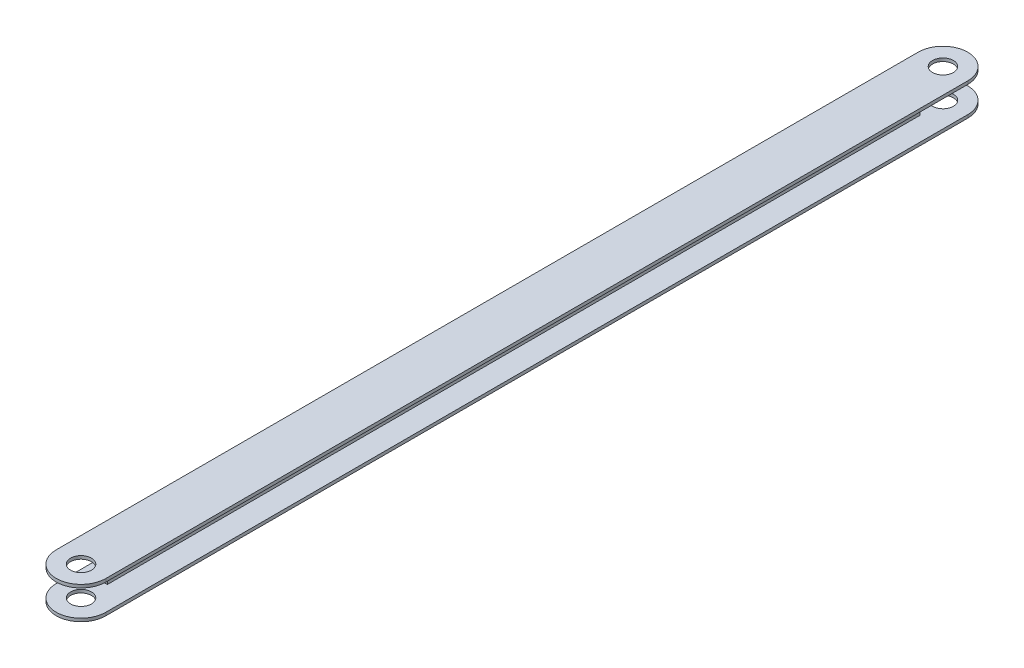
SolidWorks part; units mm, degrees
ref_plane "Front Plane" through (0, 0, 0) normal (0, 0, 1) x (1, 0, 0)
ref_plane "Top Plane" through (0, 0, 0) normal (0, 1, 0) x (1, 0, 0)
ref_plane "Right Plane" through (0, 0, 0) normal (1, 0, 0) x (0, 0, -1)
sketch "Sketch1" plane through (0, 0, 0) normal (0, 0, 1) x (1, 0, 0)
  line L0 (0, 0) -> (0, -5.6)
  line L1 (-0.6, 5) -> (0.6, 5)
  line L2 (-0.6, 5) -> (-0.6, -5)
  line L3 (-0.6, -5) -> (0.6, -5)
  line L4 (0.6, 5) -> (0.6, -5)
  line L5 (-0.6, 5) -> (0.6, -5) construction
  line L6 (-0.6, -5) -> (0.6, 5) construction
  line L7 (-9.5, -5) -> (9.5, -5)
  line L8 (-9.5, -5) -> (-9.5, -6.2)
  line L9 (-9.5, -6.2) -> (9.5, -6.2)
  line L10 (9.5, -5) -> (9.5, -6.2)
  line L11 (-9.5, -5) -> (9.5, -6.2) construction
  line L12 (-9.5, -6.2) -> (9.5, -5) construction
  line L13 (0, 0) -> (6.3315, 0) construction
  line L14 (-9.5, 6.2) -> (9.5, 5) construction
  line L15 (-9.5, 5) -> (9.5, 6.2) construction
  line L16 (9.5, 5) -> (9.5, 6.2)
  line L17 (-9.5, 6.2) -> (9.5, 6.2)
  line L18 (-9.5, 5) -> (-9.5, 6.2)
  line L19 (-9.5, 5) -> (9.5, 5)
  line L20 (-0.6, 5) -> (0.6, 5)
  point P0 (0, 0)
  point P6 (0, -5.6)
  point P19 (0, 5.6)
  dimension "D1" = 10
  dimension "D2" = 1.2
  dimension "D3" = 19
  dimension "D4" = 1.2
extrude "Boss-Extrude1" add sketch "Sketch1" along normal blind 349
sketch "Sketch3" plane through (0, 6.2, 0) normal (0, 1, 0) x (1, 0, 0)
  line L0 (-9.5, 0) -> (9.5, 0) construction
  line L1 (-14.5, -9.5) -> (-9.5, -9.5)
  line L2 (9.5, -9.5) -> (14.5, -9.5)
  line L3 (9.5, -349) -> (9.5, 0) construction
  line L4 (-9.5, -349) -> (-9.5, 0) construction
  line L12 (9.5, -9.5) -> (4, -9.5)
  line L13 (-4, -9.5) -> (-9.5, -9.5)
  line L16 (-19.5, -359) -> (19.5, -359)
  line L17 (19.5, -359) -> (19.5, 10)
  line L18 (19.5, 10) -> (-19.5, 10)
  line L19 (-19.5, 10) -> (-19.5, -359)
  line L20 (-19.5, -359) -> (19.5, -359)
  line L21 (19.5, -359) -> (19.5, 10)
  line L22 (19.5, 10) -> (-19.5, 10)
  line L23 (-19.5, 10) -> (-19.5, -359)
  arc A0 (9.5, -9.5) -> (-9.5, -9.5) centre (0, -9.5) ccw
  circle A1 centre (0, -9.5) radius 4
  arc A2 (14.5, -9.5) -> (-14.5, -9.5) centre (0, -9.5) ccw
  point P11 (9.398, -9.5)
  point P12 (0, 0)
  point P15 (0, 0)
  line M5 (9.5, 0) -> (-9.5, 0)
  line M6 (-9.5, 0) -> (-9.5, -349)
  line M8 (9.5, -349) -> (9.5, 0)
  dimension "D1" = 9.5
  dimension "D2" = 10
  dimension "D3" = 5
ref_plane "Plane4" through (0, 0, 174.5) normal (0, 0, 1) x (1, 0, 0)
extrude "Cut-Extrude2" cut sketch "Sketch3" along direction (0, 1, 0) on the side against the normal blind 370 contours A0 M5 M6 | A0 M8 M5 | L2 A2 L1 M6 M5 M8 | A1
mirror "Mirror1" about plane through (0, 0, 174.5) normal (0, 0, 1) of "Cut-Extrude2"
sketch "Sketch6" plane through (-0.6, 0, 0) normal (-1, 0, 0) x (0, 0, 1)
  line L0 (339.5, -5) -> (9.5, -5) construction
  line L1 (18.981, -5) -> (0.019, -5)
  line L2 (18.981, -5) -> (18.981, 5)
  line L3 (18.981, 5) -> (0.019, 5)
  line L4 (0.019, -5) -> (0.019, 5)
  line L5 (18.981, -5) -> (0.019, 5) construction
  line L6 (18.981, 5) -> (0.019, -5) construction
  line L7 (9.5, 5) -> (9.5, -5)
  point P0 (9.5, 0)
  point P6 (0, 0)
  point P7 (0, 0)
extrude "Cut-Extrude4" cut sketch "Sketch6" along direction (1, 0, 0) on the side against the normal blind 370
sketch "Sketch10" plane through (0, 0, 18.981) normal (0, 0, -1) x (-1, 0, 0)
  line L4 (-0.6, 5) -> (-0.6, -5)
  line L5 (-0.6, -5) -> (0.6, -5)
  line L6 (0.6, -5) -> (0.6, 5)
  line L7 (0.6, 5) -> (-0.6, 5)
  line L8 (-0.6, 5) -> (-0.6, -5)
  line L9 (-0.6, -5) -> (0.6, -5)
  line L10 (0.6, -5) -> (0.6, 5)
  line L11 (0.6, 5) -> (-0.6, 5)
  dimension "D1" = 0
extrude "Cut-Extrude5" cut sketch "Sketch10" along normal blind 105
mirror "Mirror2" about plane through (0, 0, 174.5) normal (0, 0, 1) of "Cut-Extrude5"
